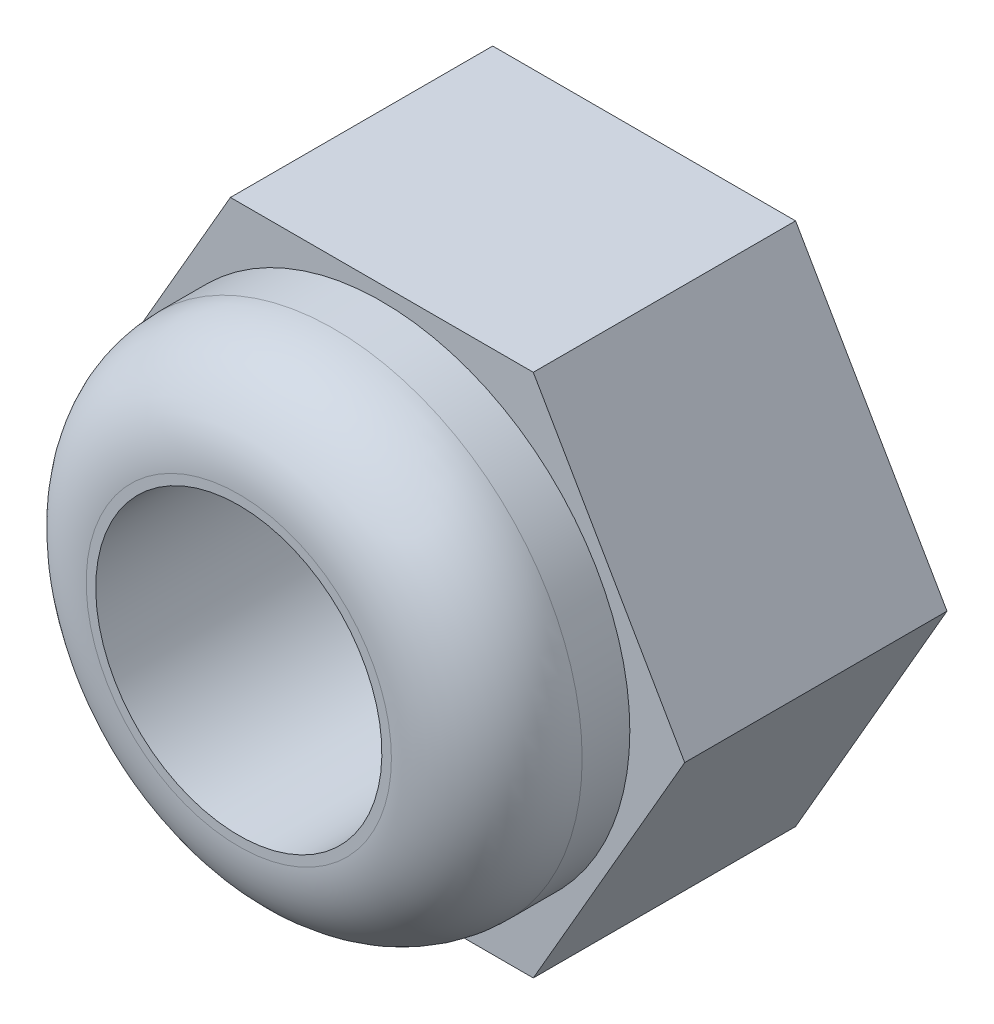
SolidWorks part; units mm, degrees
ref_plane "前视基准面" through (0, 0, 0) normal (0, 0, 1) x (1, 0, 0)
ref_plane "上视基准面" through (0, 0, 0) normal (0, 1, 0) x (1, 0, 0)
ref_plane "右视基准面" through (0, 0, 0) normal (1, 0, 0) x (0, 0, -1)
ref_plane "基准面4" through (0, 0, 2.75) normal (0, 0, 1) x (1, 0, 0)
sketch "草图1" plane through (0, 0, 2.75) normal (0, 0, 1) x (1, 0, 0)
  line L0 (1.5877, -2.75) -> (3.1754, 0)
  line L1 (3.1754, 0) -> (1.5877, 2.75)
  line L2 (1.5877, 2.75) -> (-1.5877, 2.75)
  line L3 (-1.5877, 2.75) -> (-3.1754, 0)
  line L4 (-3.1754, 0) -> (-1.5877, -2.75)
  line L5 (-1.5877, -2.75) -> (1.5877, -2.75)
extrude "凸台-拉伸1" add sketch "草图1" against normal blind 2.75
sketch "草图2" plane through (0, 0, 0) normal (0, 1, 0) x (1, 0, 0)
  line L0 (2.6, -2.75) -> (0, -2.75)
  line L1 (0, -2.75) -> (0, -4.25)
  line L2 (0, -4.25) -> (2.6, -4.25)
  line L3 (2.6, -4.25) -> (2.6, -2.75)
  line L4 (0, -2.75) -> (0, -4.25) construction
revolve "旋转1" add sketch "草图2" angle 360 about L4
hole_wizard "Ø3.0 (3) 直径孔1" positions "草图4" profile "草图3" hole size "Ø3.0" standard "Ansi Metric"
sketch "草图4" plane through (0, 0, 0) normal (0, 0, -1) x (-1, 0, 0)
  point P0 (0, 0)
sketch "草图3" plane through (0, 0, 0) normal (1, 0, 0) x (0, 1, 0)
  line L0 (0, 0) -> (0, 4.25)
  line L1 (0, 4.25) -> (1.5, 4.25)
  line L2 (1.5, 4.25) -> (1.5, 0)
  line L5 (1.5, 0) -> (0, 0)
  line L11 (0, -6.35) -> (0, 107.95) construction
  dimension "通孔孔直径" = 3
  dimension "通孔孔深度" = 4.25
fillet "圆角1" radius 1 1 edges at (2.6, 0, 4.25)
